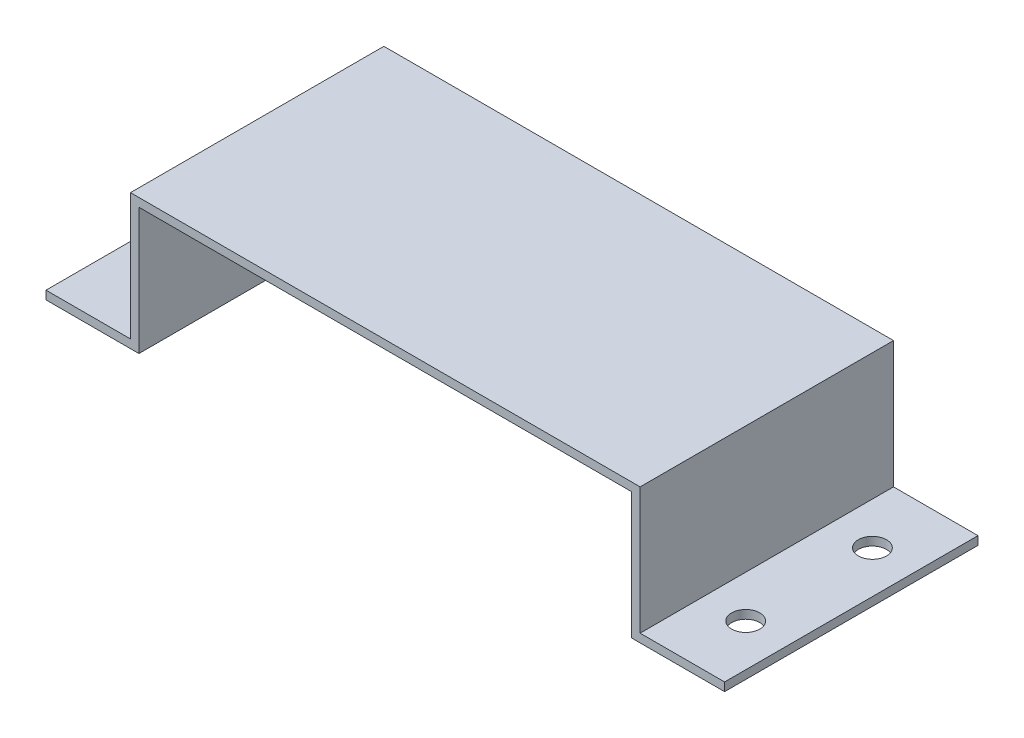
SolidWorks part; units mm, degrees
material "ABS"
ref_plane "Front Plane" through (0, 0, 0) normal (0, 0, 1) x (1, 0, 0)
ref_plane "Top Plane" through (0, 0, 0) normal (0, 1, 0) x (1, 0, 0)
ref_plane "Right Plane" through (0, 0, 0) normal (1, 0, 0) x (0, 0, -1)
sketch "Sketch1" plane through (0, 0, 0) normal (0, 0, 1) x (1, 0, 0)
  line L0 (-51.9673, 26.4243) -> (129.0327, 26.4243)
  line L5 (-48.9673, 23.4243) -> (126.0327, 23.4243)
  line L6 (-48.9673, 23.4243) -> (-48.9673, -21.5757)
  line L8 (126.0327, 23.4243) -> (126.0327, -21.5757)
  line L9 (129.0327, 26.4243) -> (129.0327, -18.5757)
  line L11 (-51.9673, 26.4243) -> (-51.9673, -18.5757)
  line L12 (-48.9673, -21.5757) -> (126.0327, -21.5757) construction
  line L13 (-51.9673, -24.5757) -> (129.0327, -24.5757) construction
  line L14 (-48.9673, -21.5757) -> (-51.9673, -21.5757)
  line L15 (126.0327, -21.5757) -> (129.0327, -21.5757)
  line L17 (-51.9673, 26.4243) -> (-51.9673, -24.5757) construction
  line L18 (129.0327, 26.4243) -> (129.0327, -24.5757) construction
  line L19 (129.0327, -18.5757) -> (159.0327, -18.5757)
  line L20 (159.0327, -18.5757) -> (159.0327, -21.5757)
  line L21 (159.0327, -21.5757) -> (129.0327, -21.5757)
  line L22 (-51.9673, -18.5757) -> (-81.9673, -18.5757)
  line L23 (-81.9673, -18.5757) -> (-81.9673, -21.5757)
  line L24 (-81.9673, -21.5757) -> (-51.9673, -21.5757)
  dimension "D1" = 3
  dimension "D2" = 175
  dimension "D3" = 126.0327
  dimension "D4" = 159.0327
  dimension "D5" = 23.4243
  dimension "D6" = 18.5757
extrude "Boss-Extrude1" add sketch "Sketch1" along normal blind 90
sketch "Sketch2" plane through (0, -18.5757, 0) normal (0, 1, 0) x (1, 0, 0)
  line L0 (144.0327, 0) -> (144.0327, -90) construction
  line L1 (159.0327, 0) -> (129.0327, 0) construction
  line L2 (159.0327, -90) -> (129.0327, -90) construction
  line L3 (159.0327, -45) -> (129.0327, -45) construction
  line L4 (159.0327, -90) -> (159.0327, 0) construction
  line L5 (129.0327, -90) -> (129.0327, 0) construction
  line L6 (38.5327, 0) -> (38.5327, -90)
  line L7 (129.0327, 0) -> (-51.9673, 0) construction
  line L8 (129.0327, -90) -> (-51.9673, -90) construction
  circle A1 centre (144.0327, -22.5) radius 5
  circle A2 centre (144.0327, -67.5) radius 5
  circle A3 centre (-66.9673, -67.5) radius 5
  circle A4 centre (-66.9673, -22.5) radius 5
  dimension "D1" = 22.5
  dimension "D2" = 10
extrude "Cut-Extrude1" cut sketch "Sketch2" against normal blind 90 contours A1 | A2 | A3 | A4
